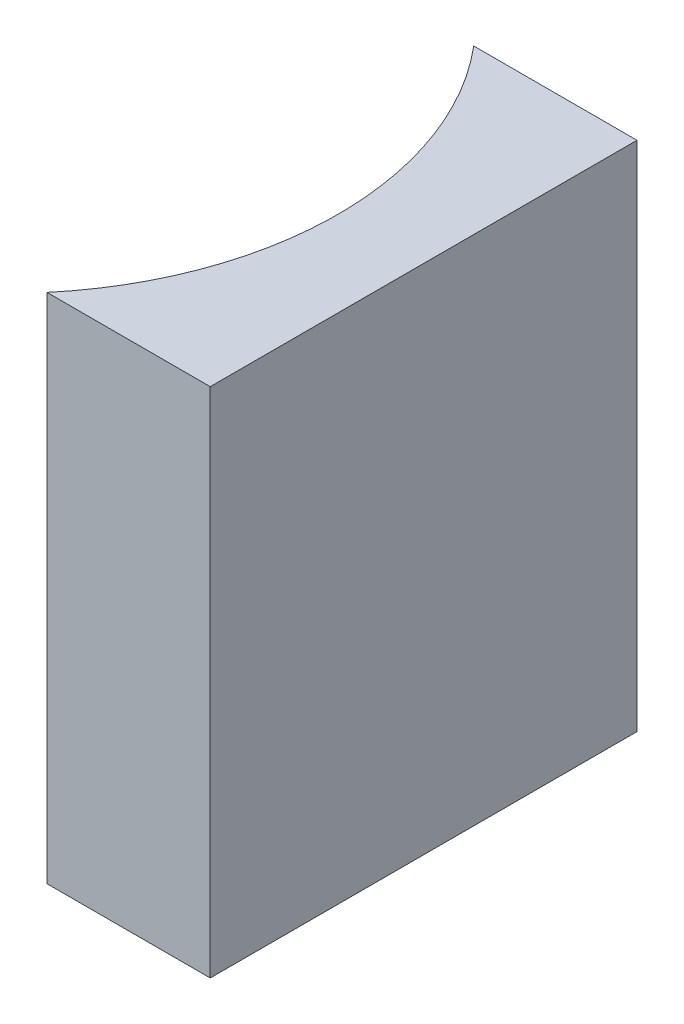
SolidWorks part; units mm, degrees
ref_plane "前视基准面" through (0, 0, 0) normal (0, 0, 1) x (1, 0, 0)
ref_plane "上视基准面" through (0, 0, 0) normal (0, 1, 0) x (1, 0, 0)
ref_plane "右视基准面" through (0, 0, 0) normal (1, 0, 0) x (0, 0, -1)
sketch "草图1" plane through (0, 0, 0) normal (0, 1, 0) x (1, 0, 0)
  line L0 (0, 0) -> (0, -10)
  line L1 (0, 0) -> (-3.8256, 0)
  line L2 (0, -10) -> (-3.8256, -10)
  line L3 (8.2336, -5) -> (-10.4405, -5) construction
  arc A0 (-3.8256, -10) -> (-3.8256, 0) centre (-9.76, -5) ccw
  point P7 (-2, -5)
  point P8 (0, -5)
  dimension "D2" = 7.76
  dimension "D3" = 2
  dimension "D1" = 10
extrude "凸台-拉伸1" add sketch "草图1" along normal blind 12
